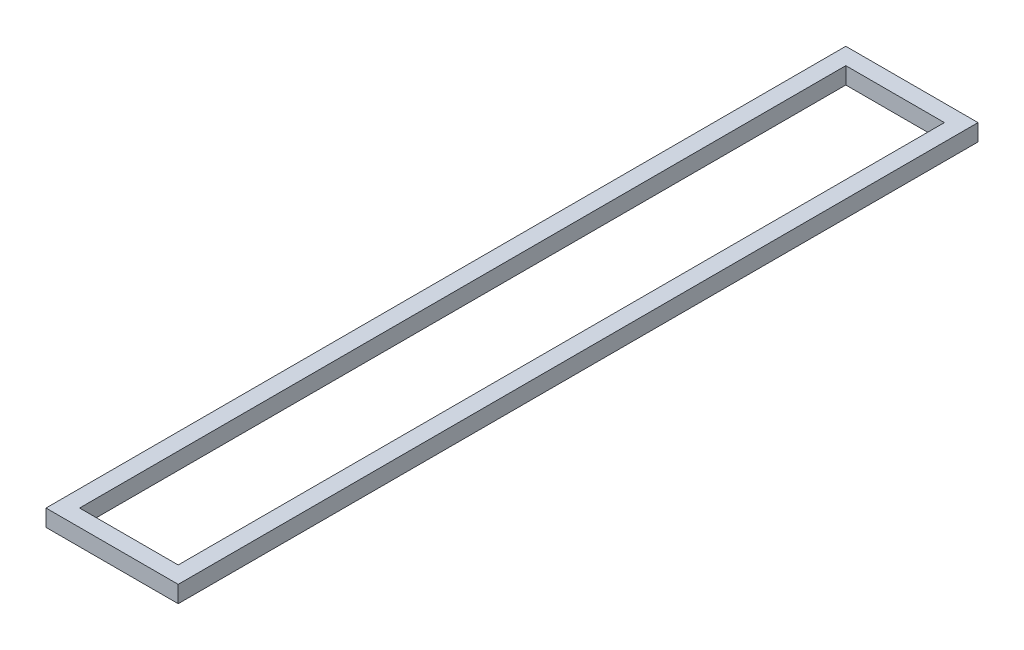
SolidWorks part; units mm, degrees
material "Ductile Iron (SN)"
ref_plane "Front Plane" through (0, 0, 0) normal (0, 0, 1) x (1, 0, 0)
ref_plane "Top Plane" through (0, 0, 0) normal (0, 1, 0) x (1, 0, 0)
ref_plane "Right Plane" through (0, 0, 0) normal (1, 0, 0) x (0, 0, -1)
sketch "Sketch1" plane through (0, 0, 0) normal (0, 1, 0) x (1, 0, 0)
  line L1 (-100, 605) -> (100, 605)
  line L2 (-100, 605) -> (-100, -605)
  line L3 (-100, -605) -> (100, -605)
  line L4 (100, 605) -> (100, -605)
  line L5 (-100, 605) -> (100, -605) construction
  line L6 (-100, -605) -> (100, 605) construction
  point P0 (0, 0)
  dimension "D1" = 1210
  dimension "D2" = 200
sketch "Sketch2" plane through (0, 0, 0) normal (1, 0, 0) x (0, 0, -1)
  line L0 (-603.8, 24.2) -> (-580.8, 24.2)
  line L1 (-605, 0) -> (-579.6, 0)
  line L2 (-605, 0) -> (-605, 25.4)
  line L3 (-605, 25.4) -> (-579.6, 25.4)
  line L4 (-579.6, 0) -> (-579.6, 25.4)
  line L5 (-580.8, 1.2) -> (-580.8, 24.2)
  line L6 (-603.8, 1.2) -> (-580.8, 1.2)
  line L7 (-603.8, 1.2) -> (-603.8, 24.2)
  dimension "D1" = 25.4
  dimension "D2" = 1.2
sweep "Sweep1" add profiles "Sketch2" path "Sketch1"
